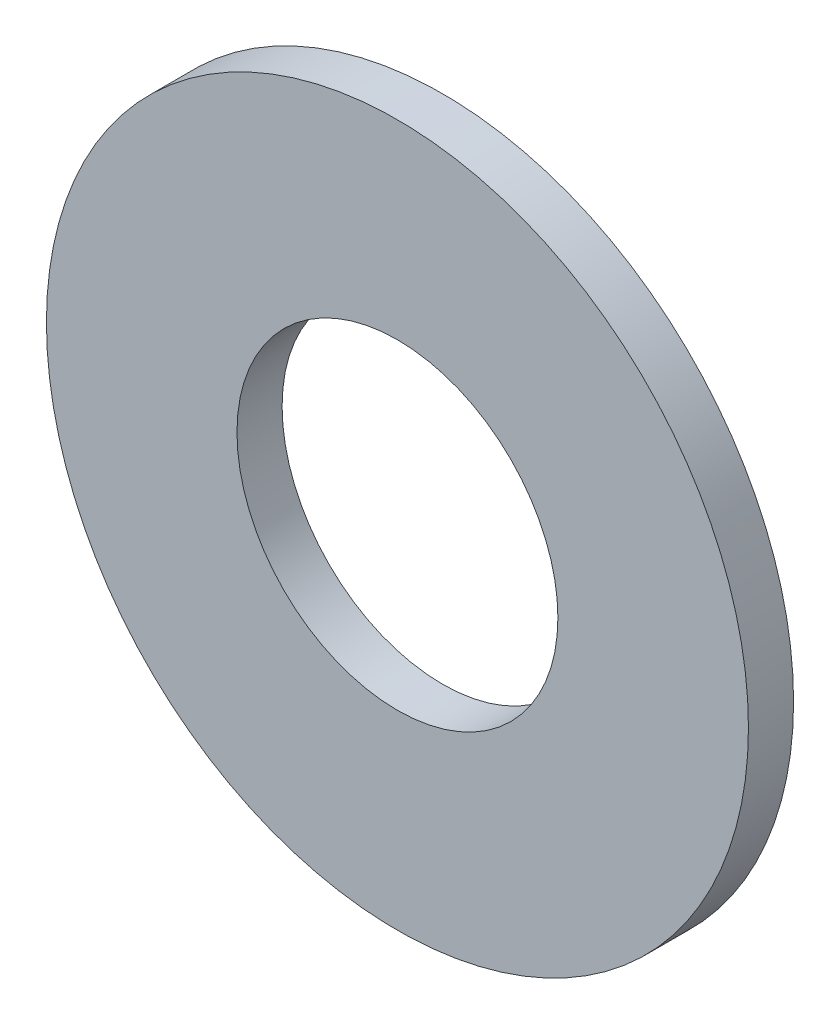
SolidWorks part; units mm, degrees
ref_plane "Front Plane" through (0, 0, 0) normal (0, 0, 1) x (1, 0, 0)
ref_plane "Top Plane" through (0, 0, 0) normal (0, 1, 0) x (1, 0, 0)
ref_plane "Right Plane" through (0, 0, 0) normal (1, 0, 0) x (0, 0, -1)
sketch "Sketch1" plane through (0, 0, 0) normal (0, 0, 1) x (1, 0, 0)
  circle A0 centre (0, 0) radius 1.6
  circle A1 centre (0, 0) radius 3.5
  dimension "ID" = 3.2
  dimension "OD" = 7
extrude "Extrude1" add sketch "Sketch1" against normal blind 0.45
